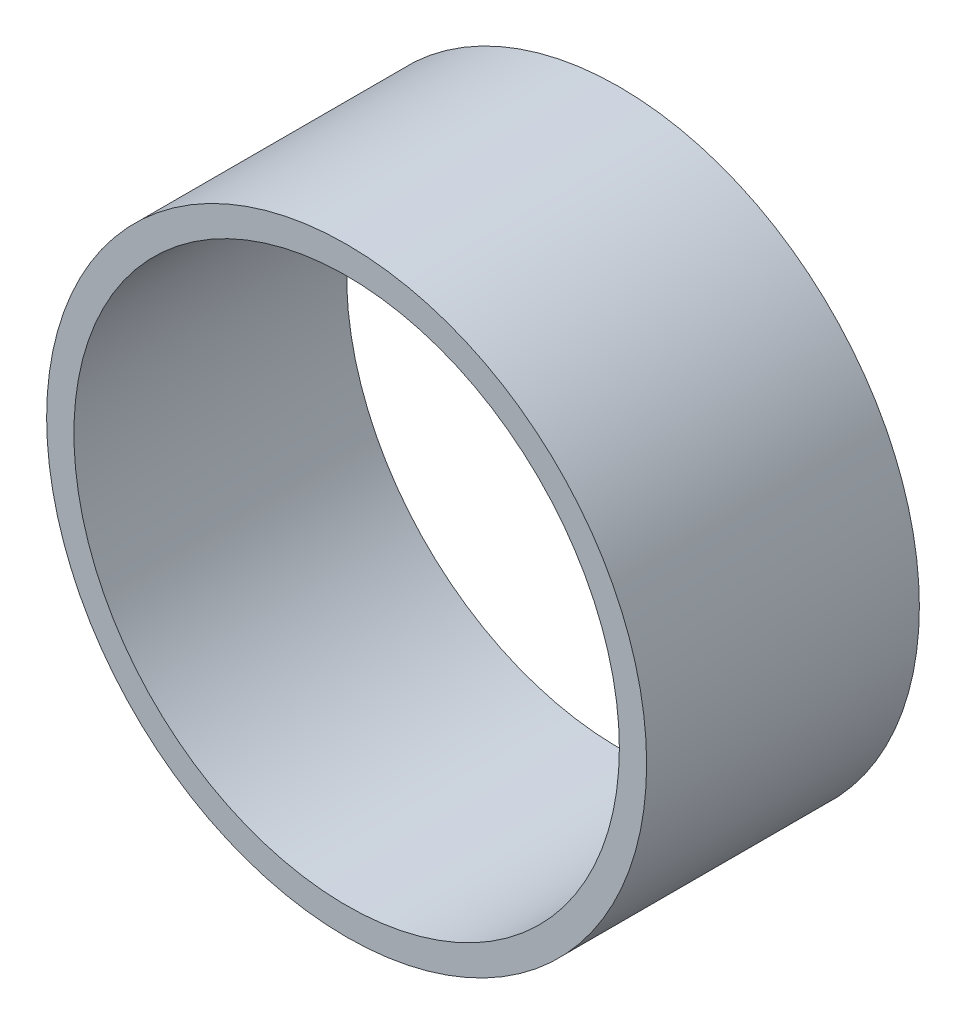
SolidWorks part; units mm, degrees
material "NEOPRENE"
ref_plane "Front Plane" through (0, 0, 0) normal (0, 0, 1) x (1, 0, 0)
ref_plane "Top Plane" through (0, 0, 0) normal (0, 1, 0) x (1, 0, 0)
ref_plane "Right Plane" through (0, 0, 0) normal (1, 0, 0) x (0, 0, -1)
sketch "Sketch1" plane through (0, 0, 0) normal (0, 0, 1) x (1, 0, 0)
  circle A0 centre (0, 0) radius 5
  circle A1 centre (0, 0) radius 5.5
  dimension "D1" = 10
  dimension "D2" = 11
extrude "Boss-Extrude1" add sketch "Sketch1" along normal blind 5
